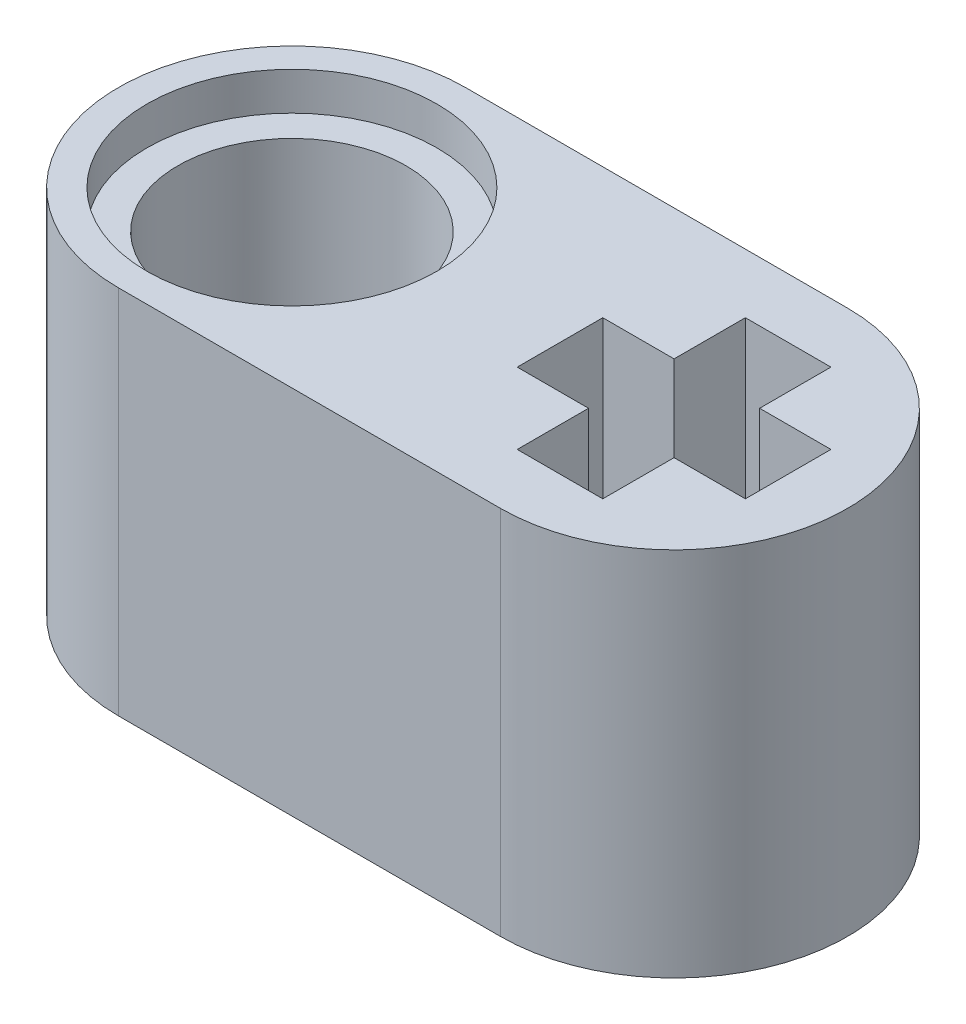
SolidWorks part; units mm, degrees
ref_plane "Front Plane" through (0, 0, 0) normal (0, 0, 1) x (1, 0, 0)
ref_plane "Top Plane" through (0, 0, 0) normal (0, 1, 0) x (1, 0, 0)
ref_plane "Right Plane" through (0, 0, 0) normal (1, 0, 0) x (0, 0, -1)
sketch "Sketch1" plane through (0, 0, 0) normal (0, 1, 0) x (1, 0, 0)
  line L0 (-4.02, 0) -> (4.02, 0) construction
  line L1 (-55, 0) -> (55, 0) construction
  line L2 (-4.02, 3.65) -> (4.02, 3.65)
  line L3 (-4.02, -3.65) -> (4.02, -3.65)
  line L4 (-7.67, 0) -> (-7.67, -5.5699) construction
  line L5 (-6.42, 0) -> (-6.42, -5.5699) construction
  line L6 (3.12, 2.4) -> (3.12, 0.9)
  line L7 (3.12, 2.4) -> (4.92, 2.4)
  line L8 (3.12, -2.4) -> (4.92, -2.4)
  line L9 (4.92, 2.4) -> (4.92, 0.9)
  line L10 (3.12, 2.4) -> (4.92, -2.4) construction
  line L11 (3.12, -2.4) -> (4.92, 2.4) construction
  line L12 (6.42, -0.9) -> (4.92, -0.9)
  line L13 (6.42, -0.9) -> (6.42, 0.9)
  line L14 (1.62, -0.9) -> (1.62, 0.9)
  line L15 (6.42, 0.9) -> (4.92, 0.9)
  line L16 (6.42, -0.9) -> (1.62, 0.9) construction
  line L17 (1.62, -0.9) -> (6.42, 0.9) construction
  line L18 (3.12, 0.9) -> (1.62, 0.9)
  line L19 (3.12, -0.9) -> (1.62, -0.9)
  line L20 (3.12, -0.9) -> (3.12, -2.4)
  line L21 (4.92, -0.9) -> (4.92, -2.4)
  arc A0 (-4.02, 3.65) -> (-4.02, -3.65) centre (-4.02, 0) ccw
  arc A1 (4.02, -3.65) -> (4.02, 3.65) centre (4.02, 0) ccw
  circle A2 centre (-4.02, 0) radius 2.4
  point P5 (0, 0)
  point P17 (4.02, 0)
  point P18 (4.02, 0)
  point P29 (7.67, 0)
  point P32 (6.42, 0)
  dimension "D3" = 1.25
  dimension "D5" = 8.04
  dimension "D1" = 7.3
  dimension "D4" = 1.25
extrude "Boss-Extrude1" add sketch "Sketch1" along normal blind 7.8
sketch "Sketch2" plane through (0, 7.8, 0) normal (0, 1, 0) x (1, 0, 0)
  circle A0 centre (-4.02, 0) radius 3.05
  circle A1 centre (-4.02, 0) radius 2.4 construction
  dimension "D1" = 0.65
extrude "Cut-Extrude1" cut sketch "Sketch2" against normal blind 0.8
sketch "Sketch4" plane through (0, 0, 0) normal (0, -1, 0) x (1, 0, 0)
  circle A0 centre (-4.02, 0) radius 3.05
extrude "Cut-Extrude2" cut sketch "Sketch4" against normal blind 0.8
